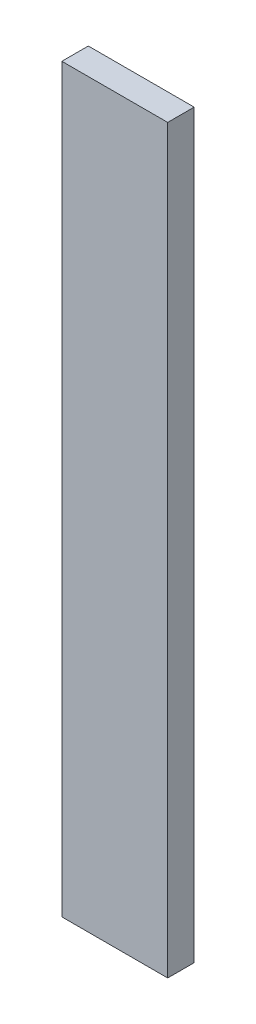
SolidWorks part; units mm, degrees
ref_plane "Front Plane" through (0, 0, 0) normal (0, 0, 1) x (1, 0, 0)
ref_plane "Top Plane" through (0, 0, 0) normal (0, 1, 0) x (1, 0, 0)
ref_plane "Right Plane" through (0, 0, 0) normal (1, 0, 0) x (0, 0, -1)
sketch "Sketch1" plane through (0, 0, 0) normal (0, 0, 1) x (1, 0, 0)
  line L1 (-12.7, 88.9) -> (12.7, 88.9)
  line L2 (-12.7, 88.9) -> (-12.7, -88.9)
  line L3 (-12.7, -88.9) -> (12.7, -88.9)
  line L4 (12.7, 88.9) -> (12.7, -88.9)
  line L5 (-12.7, 88.9) -> (12.7, -88.9) construction
  line L6 (-12.7, -88.9) -> (12.7, 88.9) construction
  point P0 (0, 0)
  dimension "D1" = 177.8
  dimension "D2" = 25.4
extrude "Boss-Extrude1" add sketch "Sketch1" along normal blind 6.35
